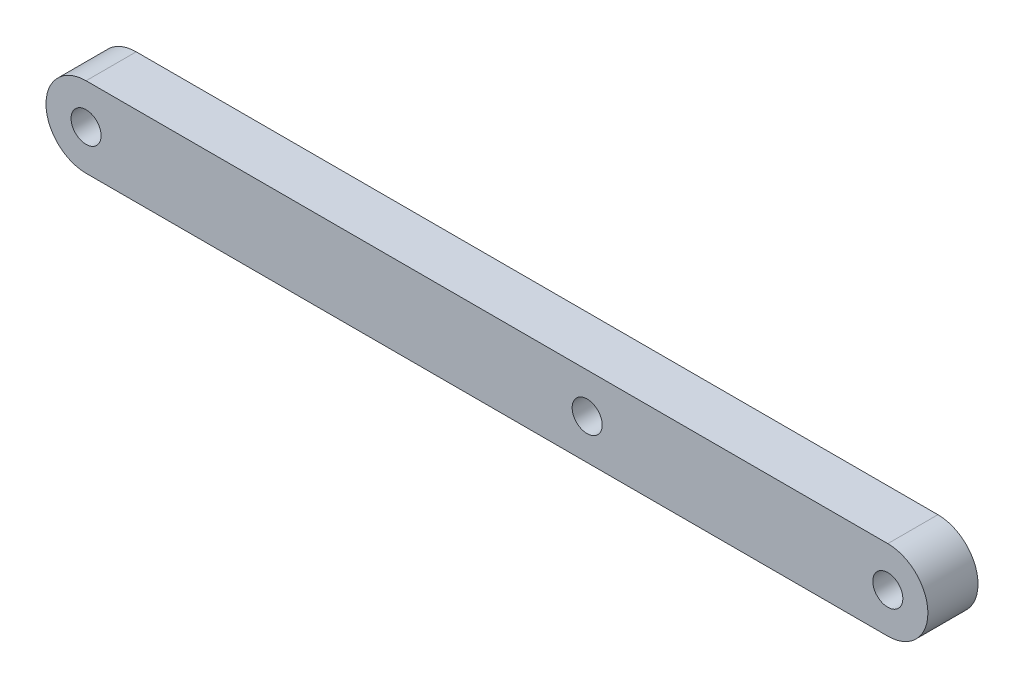
SolidWorks part; units mm, degrees
ref_plane "Front Plane" through (0, 0, 0) normal (0, 0, 1) x (1, 0, 0)
ref_plane "Top Plane" through (0, 0, 0) normal (0, 1, 0) x (1, 0, 0)
ref_plane "Right Plane" through (0, 0, 0) normal (1, 0, 0) x (0, 0, -1)
sketch "Sketch1" plane through (0, 0, 0) normal (0, 0, 1) x (1, 0, 0)
  line L1 (-97.9535, -1) -> (-17.9535, -1)
  line L3 (-97.9535, -9) -> (-17.9535, -9)
  arc A0 (-97.9535, -1) -> (-97.9535, -9) centre (-97.9535, -5) ccw
  arc A1 (-17.9535, -9) -> (-17.9535, -1) centre (-17.9535, -5) ccw
  circle A2 centre (-97.9535, -5) radius 1.5
  circle A3 centre (-17.9535, -5) radius 1.5
  point P0 (0, 0)
  dimension "D3" = 8
  dimension "D4" = 8
  dimension "D5" = 3
  dimension "D6" = 3
  dimension "D1" = 8
  dimension "D2" = 80
extrude "Boss-Extrude1" add sketch "Sketch1" along normal blind 5
sketch "Sketch2" plane through (0, 0, 5) normal (0, 0, 1) x (1, 0, 0)
  line L0 (-17.9535, -1) -> (-97.9535, -1) construction
  circle A0 centre (-47.9535, -5) radius 1.5
  circle A1 centre (-17.9535, -5) radius 1.5 construction
  dimension "D2" = 3
  dimension "D1" = 4
  dimension "D3" = 30
extrude "Cut-Extrude1" cut sketch "Sketch2" against normal blind 10
